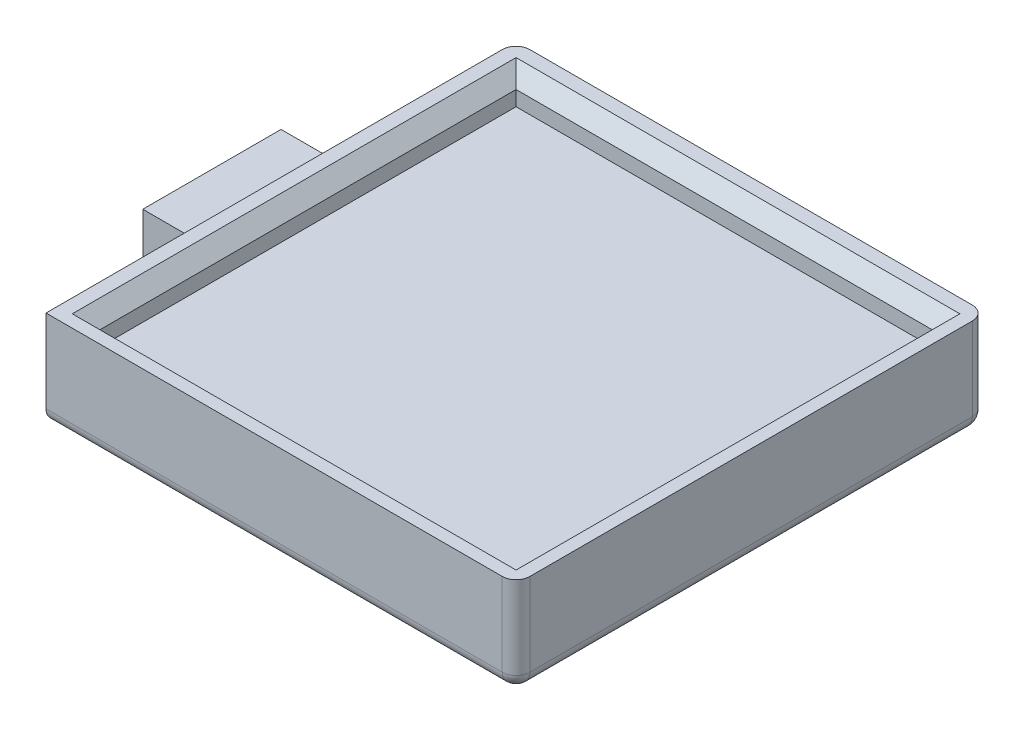
SolidWorks part; units mm, degrees
ref_plane "前视基准面" through (0, 0, 0) normal (0, 0, 1) x (1, 0, 0)
ref_plane "上视基准面" through (0, 0, 0) normal (0, 1, 0) x (1, 0, 0)
ref_plane "右视基准面" through (0, 0, 0) normal (1, 0, 0) x (0, 0, -1)
other "Configuration Table"
sketch "草图1" plane through (0, 0, 0) normal (0, 1, 0) x (1, 0, 0)
  line L0 (0, 10) -> (5, 10)
  line L1 (5, 10) -> (5, 22)
  line L2 (5, 22) -> (39, 22)
  line L3 (39, 22) -> (39, -12)
  line L4 (39, -12) -> (5, -12)
  line L5 (5, -12) -> (5, 0)
  line L6 (5, 0) -> (0, 0)
  line L7 (0, 0) -> (0, 10)
  dimension "D1" = 5
  dimension "D2" = 10
  dimension "D3" = 5
  dimension "D4" = 34
  dimension "D5" = 34
extrude "凸台-拉伸1" add sketch "草图1" along normal blind 5 contours L7 L0 L1 L2 L3 L4 L5 L6
ref_plane "基准面1" through (0, 5, 0) normal (0, 1, 0) x (1, 0, 0)
sketch "草图2" plane through (0, 5, 0) normal (0, 1, 0) x (1, 0, 0)
  line L0 (5, 10) -> (5, 22) construction
  line L1 (7, 20) -> (37.1, 20)
  line L2 (7, 20) -> (7, -10.1)
  line L3 (7, -10.1) -> (37.1, -10.1)
  line L4 (37.1, 20) -> (37.1, -10.1)
  line L6 (5, 22) -> (39, 22)
  line L7 (5, 22) -> (5, -12)
  line L8 (0, 0) -> (5, 0)
  line L9 (0, 10) -> (0, 0)
  line L10 (5, 10) -> (0, 10)
  line L11 (5, 22) -> (5, 10)
  line L12 (39, 22) -> (5, 22)
  line L13 (39, -12) -> (39, 22)
  line L14 (5, -12) -> (39, -12)
  line L15 (5, 0) -> (5, -12)
  line L16 (0, 0) -> (5, 0)
  line L17 (0, 10) -> (0, 0)
  line L18 (5, 10) -> (0, 10)
  line L19 (5, 22) -> (5, 10)
  line L20 (39, 22) -> (5, 22)
  line L21 (39, -12) -> (39, 22)
  line L22 (5, -12) -> (39, -12)
  line L23 (5, 0) -> (5, -12)
  line L24 (5, -12) -> (39, -12)
  line L25 (39, 22) -> (39, -12)
  dimension "D2" = 2
  dimension "D3" = 2
  dimension "D4" = 30.1
  dimension "D1" = 0
extrude "凸台-拉伸2" add sketch "草图2" along normal blind 2 contours L7 L22 L21 L6 L1 L4 L3 L2
ref_plane "基准面2" through (0, 7, 0) normal (0, 1, 0) x (1, 0, 0)
sketch "草图3" plane through (0, 7, 0) normal (0, 1, 0) x (1, 0, 0)
  line L1 (7, 20) -> (37.1, 20)
  line L2 (7, 20) -> (7, -10.1)
  line L3 (7, -10.1) -> (37.1, -10.1)
  line L4 (5, 22) -> (5, -12)
  line L5 (5, -12) -> (39, -12)
  line L6 (39, -12) -> (39, 22)
  line L7 (39, 22) -> (5, 22)
  line L8 (5, 22) -> (5, -12)
  line L9 (5, -12) -> (39, -12)
  line L10 (39, -12) -> (39, 22)
  line L11 (39, 22) -> (5, 22)
  line L12 (37.1, 20) -> (37.1, -10.1)
  dimension "D2" = 30.1
  dimension "D3" = 30.1
  dimension "D4" = 2
  dimension "D5" = 2
  dimension "D1" = 0
extrude "切除-拉伸2" cut sketch "草图3" against normal blind 2.08 contours L2 L1 L12 L3
chamfer "倒角1" distance 1 angle 45 4 edges at (22.05, 7, -20) (37.1, 7, -4.95) (22.05, 7, 10.1) (7, 7, -4.95)
fillet "圆角2" radius 1 6 edges at (22, 0, 12) (22, 0, -22) (39, 0, -5) (39, 3.5, 12) (5, 3.5, -22) (39, 3.5, -22)
